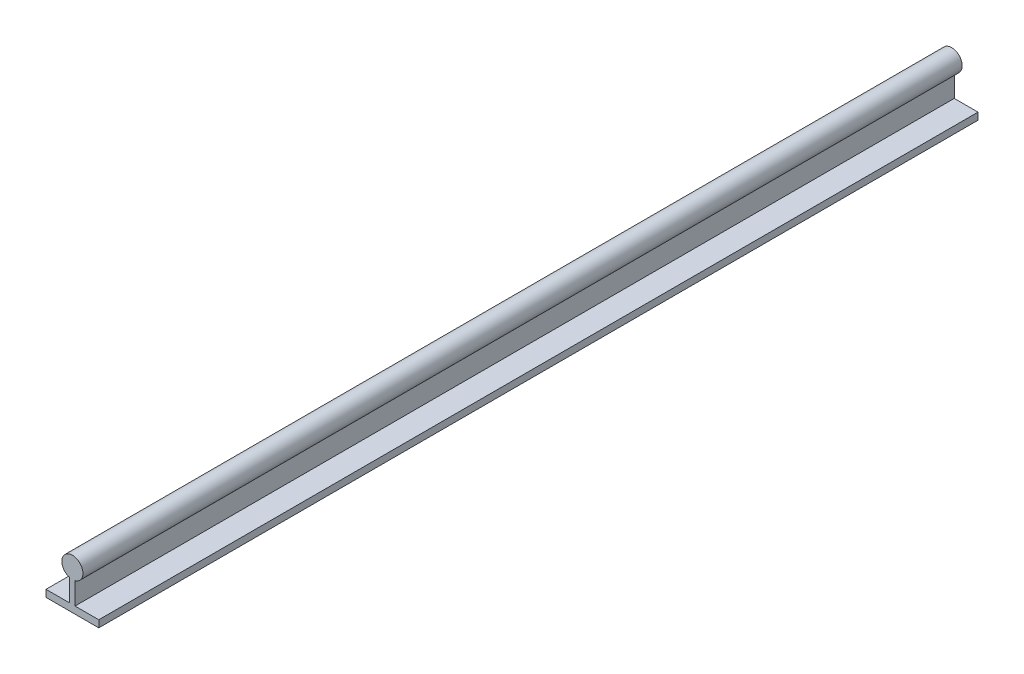
SolidWorks part; units mm, degrees
ref_plane "Front Plane" through (0, 0, 0) normal (0, 0, 1) x (1, 0, 0)
ref_plane "Top Plane" through (0, 0, 0) normal (0, 1, 0) x (1, 0, 0)
ref_plane "Right Plane" through (0, 0, 0) normal (1, 0, 0) x (0, 0, -1)
sketch "Sketch1" plane through (0, 0, 0) normal (0, 0, 1) x (1, 0, 0)
  line L0 (1.5, -18.3) -> (15, -18.3)
  line L1 (-15, -18.3) -> (-1.5, -18.3)
  line L2 (-15, -18.3) -> (-15, -22.3)
  line L3 (-15, -22.3) -> (15, -22.3)
  line L4 (15, -18.3) -> (15, -22.3)
  line L5 (-15, -18.3) -> (15, -22.3) construction
  line L6 (-15, -22.3) -> (15, -18.3) construction
  line L7 (-15.8625, 6) -> (22.6371, 6) construction
  line L8 (0, -11.1946) -> (0, -40.6) construction
  line L10 (-1.5, -5.8095) -> (-1.5, -18.3)
  line L12 (1.5, -5.8095) -> (1.5, -18.3)
  arc A0 (1.5, -5.8095) -> (-1.5, -5.8095) centre (0, 0) ccw
  point P3 (0, -20.3)
  point P9 (0, -11.1946)
  dimension "D1" = 12
  dimension "D2" = 30
  dimension "D3" = 4
  dimension "D4" = 28.3
extrude "Boss-Extrude1" add sketch "Sketch1" along normal blind 500
